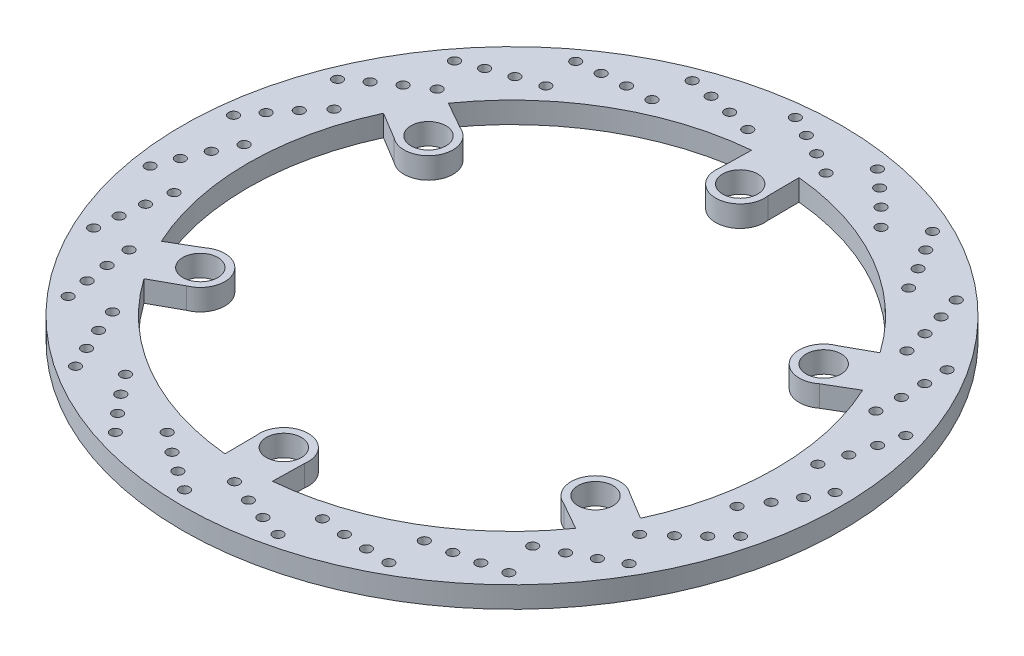
SolidWorks part; units mm, degrees
material "Alloy Steel"
ref_plane "Front" through (0, 0, 0) normal (0, 0, 1) x (1, 0, 0)
ref_plane "Top" through (0, 0, 0) normal (0, 1, 0) x (1, 0, 0)
ref_plane "Right" through (0, 0, 0) normal (1, 0, 0) x (0, 0, -1)
other "Configuration Table"
ref_plane "Plane1" through (0, 3.76, 0) normal (0, 1, 0) x (1, 0, 0)
sketch "Sketch1" plane through (0, 3.76, 0) normal (0, 1, 0) x (1, 0, 0)
  line L0 (-100.1165, -44.6604) -> (-112.8532, -52.1578)
  line L1 (-112.7848, 52.3057) -> (-100.1165, 44.6604)
  line L2 (-88.7353, 64.3732) -> (-101.5966, 71.6549)
  line L3 (-11.0944, 123.8273) -> (-11.3812, 109.0336)
  line L4 (11.3812, 109.0336) -> (11.2566, 123.8126)
  line L5 (101.6904, 71.5216) -> (88.7353, 64.3732)
  line L6 (100.1165, 44.6604) -> (112.8532, 52.1578)
  line L7 (112.7848, -52.3057) -> (100.1165, -44.6604)
  line L8 (88.7353, -64.3732) -> (101.5966, -71.6549)
  line L9 (11.0944, -123.8273) -> (11.3812, -109.0336)
  line L10 (-11.3812, -109.0336) -> (-11.2566, -123.8126)
  line L11 (-101.6904, -71.5216) -> (-88.7353, -64.3732)
  arc A0 (-88.7353, -64.3732) -> (-100.1165, -44.6604) centre (-92.998, -53.6924) ccw
  arc A1 (-112.8532, -52.1578) -> (-112.7848, 52.3057) centre (0, 0) cw
  arc A2 (-100.1165, 44.6604) -> (-88.7353, 64.3732) centre (-92.998, 53.6924) ccw
  arc A3 (-101.5966, 71.6549) -> (-11.0944, 123.8273) centre (0, 0) cw
  arc A4 (-11.3812, 109.0336) -> (11.3812, 109.0336) centre (0, 107.3848) ccw
  arc A5 (11.2566, 123.8126) -> (101.6904, 71.5216) centre (0, 0) cw
  arc A6 (88.7353, 64.3732) -> (100.1165, 44.6604) centre (92.998, 53.6924) ccw
  arc A7 (112.8532, 52.1578) -> (112.7848, -52.3057) centre (0, 0) cw
  arc A8 (100.1165, -44.6604) -> (88.7353, -64.3732) centre (92.998, -53.6924) ccw
  arc A9 (101.5966, -71.6549) -> (11.0944, -123.8273) centre (0, 0) cw
  arc A10 (11.3812, -109.0336) -> (-11.3812, -109.0336) centre (0, -107.3848) ccw
  arc A11 (-11.2566, -123.8126) -> (-101.6904, -71.5216) centre (0, 0) cw
  circle A12 centre (-92.998, -53.6924) radius 8.225
  circle A13 centre (0, -107.3848) radius 8.225
  circle A14 centre (92.998, -53.6924) radius 8.225
  circle A15 centre (92.998, 53.6924) radius 8.225
  circle A16 centre (0, 107.3848) radius 8.225
  circle A17 centre (-92.998, 53.6924) radius 8.225
  circle A18 centre (0, 0) radius 155.1
  circle A19 centre (-14.1086, 147.4535) radius 2.35
  circle A20 centre (-4.2336, 142.7542) radius 2.35
  circle A21 centre (5.6636, 137.7213) radius 2.35
  circle A22 centre (15.7722, 132.0322) radius 2.35
  circle A23 centre (26.1971, 145.792) radius 2.35
  circle A24 centre (34.438, 138.6027) radius 2.35
  circle A25 centre (42.6103, 131.0862) radius 2.35
  circle A26 centre (50.8092, 122.8808) radius 2.35
  circle A27 centre (64.5598, 133.3177) radius 2.35
  circle A28 centre (70.5555, 124.1717) radius 2.35
  circle A29 centre (76.3969, 114.729) radius 2.35
  circle A30 centre (82.0779, 104.6159) radius 2.35
  circle A31 centre (98.1345, 110.9559) radius 2.35
  circle A32 centre (101.4403, 100.5314) radius 2.35
  circle A33 centre (104.5174, 89.8629) radius 2.35
  circle A34 centre (107.2592, 78.5921) radius 2.35
  circle A35 centre (124.4309, 80.365) radius 2.35
  circle A36 centre (124.8017, 69.4352) radius 2.35
  circle A37 centre (124.8863, 58.3321) radius 2.35
  circle A38 centre (124.4857, 46.7395) radius 2.35
  circle A39 centre (141.4989, 43.8138) radius 2.35
  circle A40 centre (138.9071, 33.1893) radius 2.35
  circle A41 centre (135.993, 22.4751) radius 2.35
  circle A42 centre (132.4796, 11.4204) radius 2.35
  circle A43 centre (148.0726, 4.0131) radius 2.35
  circle A44 centre (142.7104, -5.5182) radius 2.35
  circle A45 centre (137.0137, -15.0488) radius 2.35
  circle A46 centre (130.648, -24.7456) radius 2.35
  circle A47 centre (143.6644, -36.0852) radius 2.35
  circle A48 centre (135.9295, -43.8163) radius 2.35
  circle A49 centre (127.8728, -51.4566) radius 2.35
  circle A50 centre (119.127, -59.0764) radius 2.35
  circle A51 centre (128.6012, -73.5073) radius 2.35
  circle A52 centre (119.0674, -78.8648) radius 2.35
  circle A53 centre (109.2481, -84.0481) radius 2.35
  circle A54 centre (98.7708, -89.0258) radius 2.35
  circle A55 centre (104.0003, -105.4776) radius 2.35
  circle A56 centre (93.3745, -108.0643) radius 2.35
  circle A57 centre (82.5209, -110.4062) radius 2.35
  circle A58 centre (71.0892, -112.3725) radius 2.35
  circle A59 centre (71.6862, -129.6252) radius 2.35
  circle A60 centre (60.7565, -129.2491) radius 2.35
  circle A61 centre (49.6736, -128.5759) radius 2.35
  circle A62 centre (38.1353, -127.3851) radius 2.35
  circle A63 centre (34.0554, -144.159) radius 2.35
  circle A64 centre (23.6325, -140.8482) radius 2.35
  circle A65 centre (13.1422, -137.2097) radius 2.35
  circle A66 centre (2.3531, -132.9501) radius 2.35
  circle A67 centre (-6.1011, -148.0012) radius 2.35
  circle A68 centre (-15.2442, -142.0011) radius 2.35
  circle A69 centre (-24.3639, -135.6674) radius 2.35
  circle A70 centre (-33.6037, -128.6548) radius 2.35
  circle A71 centre (-45.8051, -140.8669) radius 2.35
  circle A72 centre (-52.9903, -132.6225) radius 2.35
  circle A73 centre (-60.063, -124.0631) radius 2.35
  circle A74 centre (-67.0682, -114.8177) radius 2.35
  circle A75 centre (-82.112, -123.2851) radius 2.35
  circle A76 centre (-86.8064, -113.4079) radius 2.35
  circle A77 centre (-91.3076, -103.2577) radius 2.35
  circle A78 centre (-95.5586, -92.4652) radius 2.35
  circle A79 centre (-112.3289, -96.5598) radius 2.35
  circle A80 centre (-114.1845, -85.7823) radius 2.35
  circle A81 centre (-115.7802, -74.7942) radius 2.35
  circle A82 centre (-116.9618, -63.2549) radius 2.35
  circle A83 centre (-134.215, -62.6731) radius 2.35
  circle A84 centre (-133.094, -51.7946) radius 2.35
  circle A85 centre (-131.666, -40.7835) radius 2.35
  circle A86 centre (-129.6906, -29.3534) radius 2.35
  circle A87 centre (-146.147, -24.1383) radius 2.35
  circle A88 centre (-142.1325, -13.9656) radius 2.35
  circle A89 centre (-137.7867, -3.748) radius 2.35
  circle A90 centre (-132.8007, 6.7252) radius 2.35
  circle A91 centre (-147.2399, 16.1868) radius 2.35
  circle A92 centre (-140.6298, 24.8992) radius 2.35
  circle A93 centre (-133.6884, 33.5654) radius 2.35
  circle A94 centre (-126.0617, 42.3051) radius 2.35
  circle A95 centre (-137.4127, 55.3114) radius 2.35
  circle A96 centre (-128.6971, 61.9173) radius 2.35
  circle A97 centre (-119.6751, 68.3894) radius 2.35
  circle A98 centre (-109.9732, 74.7473) radius 2.35
  circle A99 centre (-117.3942, 90.3338) radius 2.35
  circle A100 centre (-107.2196, 94.3433) radius 2.35
  circle A101 centre (-96.786, 98.1413) radius 2.35
  circle A102 centre (-85.7285, 101.6459) radius 2.35
  circle A103 centre (-88.6691, 118.6566) radius 2.35
  circle A104 centre (-77.7901, 119.7723) radius 2.35
  circle A105 centre (-66.7187, 120.6145) radius 2.35
  circle A106 centre (-55.1257, 121.0058) radius 2.35
  circle A107 centre (-53.3679, 138.1791) radius 2.35
  circle A108 centre (-42.5912, 136.3183) radius 2.35
  circle A109 centre (-31.7032, 134.1422) radius 2.35
  circle A110 centre (-20.4345, 131.3914) radius 2.35
extrude "Boss-Extrude1" add sketch "Sketch1" against normal blind 10
